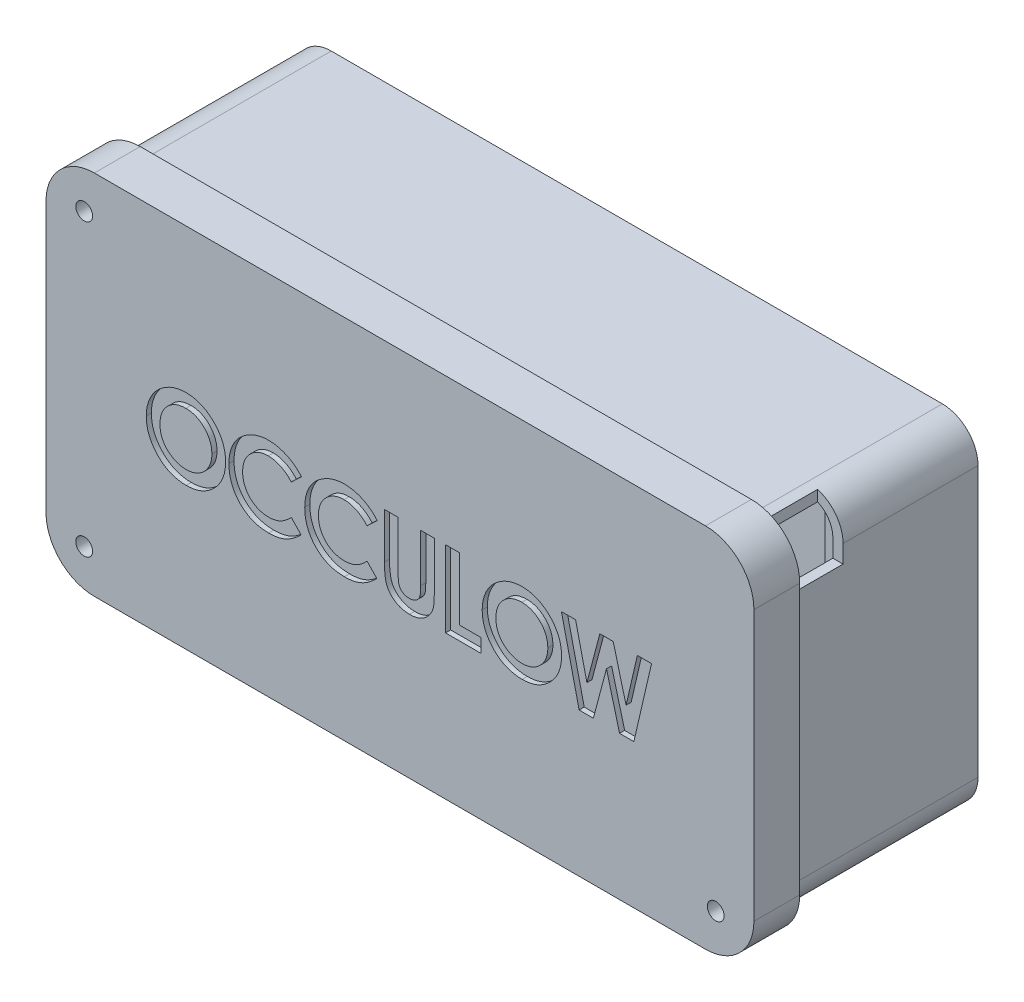
SolidWorks part; units mm, degrees
ref_plane "Front Plane" through (0, 0, 0) normal (0, 0, 1) x (1, 0, 0)
ref_plane "Top Plane" through (0, 0, 0) normal (0, 1, 0) x (1, 0, 0)
ref_plane "Right Plane" through (0, 0, 0) normal (1, 0, 0) x (0, 0, -1)
sketch "Sketch1" plane through (0, 0, 0) normal (0, 1, 0) x (1, 0, 0)
  line L0 (0, 7.5) -> (-65, 7.5) construction
  line L1 (-5, -3.5) -> (5, -3.5)
  line L2 (-5, -3.5) -> (-5, 3.5)
  line L3 (-5, 3.5) -> (5, 3.5)
  line L4 (5, -3.5) -> (5, 3.5)
  line L5 (-5, 0) -> (0, 0) construction
  line L6 (0, 0) -> (0, 15) construction
  line L7 (-65, 27.5) -> (65, 27.5)
  line L8 (-65, 27.5) -> (-65, -12.5)
  line L9 (-65, -12.5) -> (65, -12.5)
  line L10 (65, 27.5) -> (65, -12.5)
  circle A0 centre (0, 15) radius 5.5
  point P10 (0, -3.5)
  point P16 (0, 27.5)
  dimension "D1" = 11
  dimension "D2" = 10
  dimension "D3" = 7
  dimension "D4" = 15
  dimension "D5" = 130
  dimension "D6" = 40
extrude "Boss-Extrude1" add sketch "Sketch1" against normal blind 2
sketch "Sketch2" plane through (0, 0, -27.5) normal (0, 0, -1) x (-1, 0, 0)
  line L0 (35, 45.5) -> (35, 15.5) construction
  line L1 (65, -2) -> (-65, -2)
  line L2 (65, -2) -> (65, 63)
  line L3 (65, 63) -> (-65, 63)
  line L4 (-65, -2) -> (-65, 63)
  line L5 (-15, 56) -> (-45, 56) construction
  line L6 (-15, 56) -> (-15, 14) construction
  line L7 (-15, 14) -> (-45, 14) construction
  line L8 (-45, 56) -> (-45, 14) construction
  line L9 (65, 30.5) -> (35, 30.5) construction
  line L10 (35, 30.5) -> (-15, 30.5) construction
  circle A0 centre (-15, 56) radius 1
  circle A1 centre (-45, 56) radius 1
  circle A2 centre (-45, 14) radius 1
  circle A3 centre (-15, 14) radius 1
  circle A4 centre (35, 45.5) radius 1
  circle A5 centre (35, 15.5) radius 1
  dimension "D4" = 2
  dimension "D1" = 30
  dimension "D2" = 42
  dimension "D3" = 65
  dimension "D5" = 30
  dimension "D6" = 7
  dimension "D7" = 20
  dimension "D8" = 30
extrude "Boss-Extrude2" add sketch "Sketch2" along normal blind 3.5
sketch "Sketch4" plane through (0, 0, -27.5) normal (0, 0, 1) x (1, 0, 0)
  circle A0 centre (15, 56) radius 1 construction
  circle A1 centre (45, 56) radius 1 construction
  circle A2 centre (15, 14) radius 1 construction
  circle A3 centre (45, 14) radius 1 construction
  circle A4 centre (15, 56) radius 1
  circle A5 centre (45, 56) radius 1
  circle A6 centre (15, 14) radius 1
  circle A7 centre (45, 14) radius 1
  circle A8 centre (15, 56) radius 3.5
  circle A9 centre (45, 56) radius 3.5
  circle A10 centre (15, 14) radius 3.5
  circle A11 centre (45, 14) radius 3.5
  dimension "D1" = 2.5
extrude "Boss-Extrude3" add sketch "Sketch4" along normal blind 2.5
sketch "Sketch5" plane through (65, 0, 0) normal (1, 0, 0) x (0, 0, -1)
  line L1 (-12.5, -2) -> (31, -2)
  line L2 (-12.5, -2) -> (-12.5, 63)
  line L3 (-12.5, 63) -> (31, 63)
  line L4 (31, -2) -> (31, 63)
extrude "Boss-Extrude4" add sketch "Sketch5" along normal blind 2
sketch "Sketch6" plane through (0, 0, 12.5) normal (0, 0, 1) x (1, 0, 0)
  line L0 (55.5, 9) -> (55.5, 0)
  line L2 (65, -2) -> (65, 63) construction
  line L3 (55.5, 9) -> (55.5, 14)
  line L4 (55.5, 14) -> (58.5, 14)
  line L5 (58.5, 14) -> (58.5, 12)
  line L6 (58.5, 12) -> (65, 12)
  line L7 (65, 12) -> (65, 0)
  line L8 (-65, 63) -> (65, 63) construction
  line L9 (-65, 0) -> (65, 0) construction
  line L10 (55.5, 0) -> (65, 0)
  line L12 (-65, 63) -> (-58.5, 63)
  line L13 (-65, 63) -> (-65, 56.5)
  line L14 (-65, 56.5) -> (-58.5, 56.5)
  line L15 (-58.5, 63) -> (-58.5, 56.5)
  line L16 (-65, 0) -> (-58.5, 0)
  line L17 (-65, 0) -> (-65, 6.5)
  line L18 (-65, 6.5) -> (-58.5, 6.5)
  line L19 (-58.5, 0) -> (-58.5, 6.5)
  dimension "D1" = 6.5
  dimension "D2" = 2
  dimension "D3" = 3
  dimension "D4" = 5
  dimension "D5" = 50
  dimension "D6" = 51
extrude "Boss-Extrude5" add sketch "Sketch6" against normal up to surface (40 mm away) up to face at (11.5, 14, -27.5)
sketch "Sketch7" plane through (-65, 0, 0) normal (-1, 0, 0) x (0, 0, 1)
  line L1 (12.5, -2) -> (-31, -2)
  line L2 (12.5, -2) -> (12.5, 63)
  line L3 (12.5, 63) -> (-31, 63)
  line L4 (-31, -2) -> (-31, 63)
extrude "Boss-Extrude6" add sketch "Sketch7" along normal blind 2
sketch "Sketch8" plane through (0, 63, 0) normal (0, 1, 0) x (1, 0, 0)
  line L1 (-67, 31) -> (67, 31)
  line L2 (-67, 31) -> (-67, -12.5)
  line L3 (-67, -12.5) -> (67, -12.5)
  line L4 (67, 31) -> (67, -12.5)
extrude "Boss-Extrude7" add sketch "Sketch8" along normal blind 2
sketch "Sketch12" plane through (0, 0, -27.5) normal (0, 0, 1) x (1, 0, 0)
  line L1 (55.5, 0) -> (65, 0)
  line L2 (55.5, 0) -> (55.5, 63)
  line L3 (55.5, 63) -> (65, 63)
  line L4 (65, 0) -> (65, 63)
extrude "Boss-Extrude10" add sketch "Sketch12" along normal offset from surface (15 mm away) 25 up to face at (0, 31.5, 12.5)
sketch "Sketch9" plane through (0, 0, 12.5) normal (0, 0, 1) x (1, 0, 0)
  line L1 (67, 65) -> (62, 65)
  line L2 (67, 65) -> (67, 54.5)
  line L3 (67, 54.5) -> (62, 54.5)
  line L4 (62, 65) -> (62, 54.5)
  line L5 (65, 63) -> (65, 12) construction
  dimension "D1" = 10.5
  dimension "D2" = 3
extrude "Cut-Extrude1" cut sketch "Sketch9" against normal offset from surface (17 mm away) 8 up to face at (59.6667, 29.6667, -12.5)
sketch "Sketch10" plane through (0, 0, -27.5) normal (0, 0, 1) x (1, 0, 0)
  line L0 (0, 0) -> (0, 5.1432) construction
  line L1 (-14.75, 0) -> (-6.75, 8)
  line L2 (-6.75, 8) -> (-4.7, 5)
  line L3 (-6.75, 0) -> (-14.75, 0)
  line L4 (-4.7, 5) -> (-6.75, 5)
  line L5 (-6.75, 5) -> (-6.75, 0)
  line L6 (55.5, 0) -> (-58.5, 0) construction
  line L7 (4.7, 5) -> (6.75, 5)
  line L8 (6.75, 8) -> (4.7, 5)
  line L9 (14.75, 0) -> (6.75, 8)
  line L10 (6.75, 0) -> (14.75, 0)
  line L11 (6.75, 5) -> (6.75, 0)
  dimension "D1" = 13.5
  dimension "D2" = 9.4
  dimension "D3" = 3
  dimension "D4" = 45
  dimension "D5" = 5
extrude "Boss-Extrude8" add sketch "Sketch10" along normal blind 18
sketch "Sketch11" plane through (0, 0, -27.5) normal (0, 0, 1) x (1, 0, 0)
  line L0 (0, 0) -> (0, 9.1996) construction
  line L1 (-21, 0) -> (-21, 5)
  line L2 (-14.75, 0) -> (-58.5, 0) construction
  line L3 (-21, 5) -> (-18.25, 5)
  line L4 (-18.25, 5) -> (-21, 8)
  line L5 (-21, 8) -> (-29, 0)
  line L6 (-29, 0) -> (-21, 0)
  line L7 (29, 0) -> (21, 0)
  line L8 (21, 8) -> (29, 0)
  line L9 (18.25, 5) -> (21, 8)
  line L10 (21, 5) -> (18.25, 5)
  line L11 (21, 0) -> (21, 5)
  dimension "D1" = 45
  dimension "D2" = 42
  dimension "D3" = 5
  dimension "D4" = 36.5
  dimension "D5" = 3
extrude "Boss-Extrude9" add sketch "Sketch11" along normal up to surface (40 mm away) up to face at (0.0417, 29.5556, 12.5)
sketch "Sketch13" plane through (0, 0, 12.5) normal (0, 0, 1) x (1, 0, 0)
  line L0 (-62, 60) -> (-62, 3) construction
  line L1 (-62, 3) -> (62, 3) construction
  line L2 (62, 3) -> (62, 60) construction
  line L3 (62, 60) -> (-62, 60) construction
  line L4 (-67, -2) -> (-67, 65) construction
  line L5 (-67, -2) -> (67, -2) construction
  line L6 (67, 54.5) -> (67, -2) construction
  line L7 (-67, 65) -> (62, 65) construction
  circle A0 centre (-62, 60) radius 1
  circle A1 centre (-62, 3) radius 1
  circle A2 centre (62, 3) radius 1
  dimension "D5" = 2
  dimension "D1" = 5
  dimension "D2" = 5
  dimension "D3" = 5
  dimension "D4" = 5
extrude "Cut-Extrude2" cut sketch "Sketch13" against normal blind 25
fillet "Fillet1" radius 5 11 edges at (55.5, 0, -7.5) (-58.5, 0, -7.5) (55.5, 63, -20) (14.75, 0, -18.5) (-14.75, 0, -18.5) (29, 0, -7.5) (-29, 0, -7.5)
fillet "Fillet2" radius 7 6 edges at (67, 65, -17.75) (67, -2, -9.25) (-67, 65, -9.25) (-58.5, 56.5, -7.5) (-58.5, 6.5, -7.5) (-67, -2, -9.25)
fillet "Fillet3" radius 1 4 edges at (21, 8, -7.5) (-21, 8, -7.5) (6.75, 8, -18.5) (-6.75, 8, -18.5)
sketch "Sketch14" plane through (0, 0, 12.5) normal (0, 0, 1) x (1, 0, 0)
  line L0 (60, 67.5) -> (-60, 67.5)
  line L1 (-69.5, 58) -> (-69.5, 5)
  line L2 (-60, -4.5) -> (60, -4.5)
  line L3 (69.5, 5) -> (69.5, 58)
  line L4 (60, 65) -> (-60, 65)
  line L5 (67, 5) -> (67, 58)
  line L6 (-60, -2) -> (60, -2)
  line L7 (-67, 58) -> (-67, 5)
  line L8 (60, 65) -> (-60, 65) construction
  line L9 (67, 5) -> (67, 58) construction
  line L10 (-60, -2) -> (60, -2) construction
  line L11 (-67, 58) -> (-67, 5) construction
  line L12 (60, 65.5) -> (-60, 65.5)
  line L13 (-67.5, 58) -> (-67.5, 5)
  line L14 (-60, -2.5) -> (60, -2.5)
  line L15 (67.5, 5) -> (67.5, 58)
  arc A0 (-60, 67.5) -> (-69.5, 58) centre (-60, 58) ccw
  arc A1 (-69.5, 5) -> (-60, -4.5) centre (-60, 5) ccw
  arc A2 (60, -4.5) -> (69.5, 5) centre (60, 5) ccw
  arc A3 (69.5, 58) -> (60, 67.5) centre (60, 58) ccw
  arc A4 (67, 58) -> (60, 65) centre (60, 58) ccw
  arc A5 (60, -2) -> (67, 5) centre (60, 5) ccw
  arc A6 (-67, 5) -> (-60, -2) centre (-60, 5) ccw
  arc A7 (-60, 65) -> (-67, 58) centre (-60, 58) ccw
  arc A8 (67, 58) -> (60, 65) centre (60, 58) ccw construction
  arc A9 (60, -2) -> (67, 5) centre (60, 5) ccw construction
  arc A10 (-67, 5) -> (-60, -2) centre (-60, 5) ccw construction
  arc A11 (-60, 65) -> (-67, 58) centre (-60, 58) ccw construction
  arc A12 (-60, 65.5) -> (-67.5, 58) centre (-60, 58) ccw
  arc A13 (-67.5, 5) -> (-60, -2.5) centre (-60, 5) ccw
  arc A14 (60, -2.5) -> (67.5, 5) centre (60, 5) ccw
  arc A15 (67.5, 58) -> (60, 65.5) centre (60, 58) ccw
  dimension "D1" = 0
  dimension "D2" = 2.5
  dimension "D3" = 0.5
extrude "Boss-Extrude11" add sketch "Sketch14" against normal blind 6 separate body
sketch "Sketch15" plane through (0, 0, 12.5) normal (0, 0, 1) x (1, 0, 0)
  line L4 (60, 67.5) -> (-60, 67.5)
  line L5 (-69.5, 58) -> (-69.5, 5)
  line L6 (-60, -4.5) -> (60, -4.5)
  line L7 (69.5, 5) -> (69.5, 58)
  line L8 (60, 67.5) -> (-60, 67.5)
  line L9 (-69.5, 58) -> (-69.5, 5)
  line L10 (-60, -4.5) -> (60, -4.5)
  line L11 (69.5, 5) -> (69.5, 58)
  circle A0 centre (62, 3) radius 1.65
  circle A1 centre (-62, 3) radius 1.65
  circle A2 centre (-62, 60) radius 1.65
  arc A4 (69.5, 58) -> (60, 67.5) centre (60, 58) ccw
  arc A5 (-60, 67.5) -> (-69.5, 58) centre (-60, 58) ccw
  arc A6 (-69.5, 5) -> (-60, -4.5) centre (-60, 5) ccw
  arc A7 (60, -4.5) -> (69.5, 5) centre (60, 5) ccw
  arc A8 (69.5, 58) -> (60, 67.5) centre (60, 58) ccw
  arc A9 (-60, 67.5) -> (-69.5, 58) centre (-60, 58) ccw
  arc A10 (-69.5, 5) -> (-60, -4.5) centre (-60, 5) ccw
  arc A11 (60, -4.5) -> (69.5, 5) centre (60, 5) ccw
  dimension "D2" = 3.3
  dimension "D1" = 0
extrude "Boss-Extrude12" add sketch "Sketch15" along normal blind 3
sketch "Sketch16" plane through (0, 0, 15.5) normal (0, 0, 1) x (1, 0, 0)
  line L0 (-69.5, 31.5) -> (69.5, 31.5) construction
  line L1 (-69.5, 58) -> (-69.5, 5) construction
  line L2 (69.5, 5) -> (69.5, 58) construction
  line L3 (0, 67.5) -> (0, -4.5) construction
  line L4 (60, 67.5) -> (-60, 67.5) construction
  line L5 (-60, -4.5) -> (60, -4.5) construction
  text T0 "<b>OCCULOW</b>" font "Century Gothic" height 15
extrude "Cut-Extrude3" cut sketch "Sketch16" against normal blind 1
